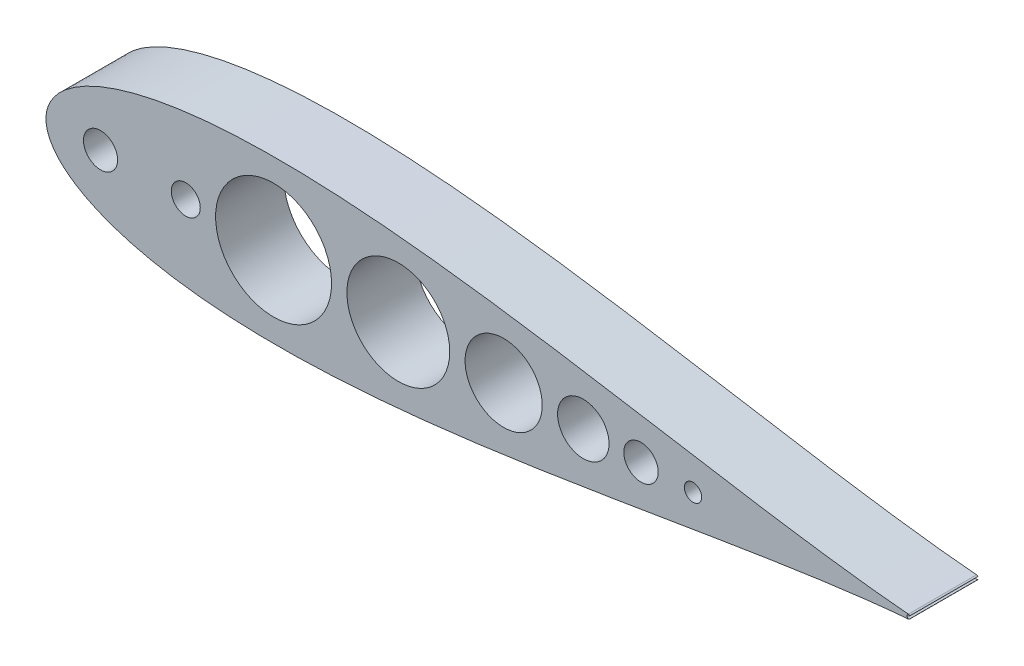
SolidWorks part; units mm, degrees
material "Polyurethane Foam Rigid"
ref_plane "Front Plane" through (0, 0, 0) normal (0, 0, 1) x (1, 0, 0)
ref_plane "Top Plane" through (0, 0, 0) normal (0, 1, 0) x (1, 0, 0)
ref_plane "Right Plane" through (0, 0, 0) normal (1, 0, 0) x (0, 0, -1)
curve "Curve4"
  spline degree 3 poles (100, 0, 0) (99.8498, 0.0023, 0) (99.4759, 0.008, 0) (99.1023, 0.0238, 0) (98.8789, 0.0332, 0) knots 0 0 0 0 0.401829 1 1 1 1
curve "Curve5"
  spline degree 3 poles (99.3714, -0.0082, 0) (100.2526, 0, 0) (99.3714, 0.0082, 0) (98.8504, 0.035, 0) (97.904, 0.0811, 0) (96.8285, 0.1543, 0) (95.5159, 0.2583, 0) (94.013, 0.3972, 0) (92.313, 0.574, 0) (90.4281, 0.791, 0) (88.3655, 1.0495, 0) (86.1348, 1.3497, 0) (83.7456, 1.691, 0) (81.2082, 2.0715, 0) (78.5335, 2.4886, 0) (75.7326, 2.9386, 0) (72.8172, 3.4168, 0) (69.799, 3.9177, 0) (66.6904, 4.435, 0) (63.5039, 4.9616, 0) (60.2521, 5.4899, 0) (56.948, 6.0119, 0) (53.6049, 6.519, 0) (50.2363, 7.0024, 0) (46.8558, 7.4534, 0) (43.4774, 7.8632, 0) (40.1152, 8.2232, 0) (36.7837, 8.5249, 0) (33.4975, 8.7606, 0) (30.2716, 8.923, 0) (27.1211, 9.0055, 0) (24.0614, 9.0025, 0) (21.108, 8.909, 0) (18.277, 8.7213, 0) (15.5843, 8.4369, 0) (13.0466, 8.0543, 0) (10.6806, 7.5735, 0) (8.5039, 6.996, 0) (6.5349, 6.3253, 0) (4.7933, 5.5673, 0) (3.3001, 4.7321, 0) (2.0777, 3.8366, 0) (1.1467, 2.91, 0) (0.5165, 2.0014, 0) (0.165, 1.1816, 0) (0.0231, 0.524, 0) (-0.0093, 0, 0) (0.0231, -0.524, 0) (0.165, -1.1816, 0) (0.5165, -2.0014, 0) (1.1467, -2.91, 0) (2.0777, -3.8366, 0) (3.3001, -4.7321, 0) (4.7933, -5.5673, 0) (6.5349, -6.3253, 0) (8.5039, -6.996, 0) (10.6806, -7.5735, 0) (13.0466, -8.0543, 0) (15.5843, -8.4369, 0) (18.277, -8.7213, 0) (21.108, -8.909, 0) (24.0614, -9.0025, 0) (27.1211, -9.0055, 0) (30.2716, -8.923, 0) (33.4975, -8.7606, 0) (36.7837, -8.5249, 0) (40.1152, -8.2232, 0) (43.4774, -7.8632, 0) (46.8558, -7.4534, 0) (50.2363, -7.0024, 0) (53.6049, -6.519, 0) (56.948, -6.0119, 0) (60.2521, -5.4899, 0) (63.5039, -4.9616, 0) (66.6904, -4.435, 0) (69.799, -3.9177, 0) (72.8172, -3.4168, 0) (75.7326, -2.9386, 0) (78.5335, -2.4886, 0) (81.2082, -2.0715, 0) (83.7456, -1.691, 0) (86.1348, -1.3497, 0) (88.3655, -1.0495, 0) (90.4281, -0.791, 0) (92.313, -0.574, 0) (94.013, -0.3972, 0) (95.5159, -0.2583, 0) (96.8285, -0.1543, 0) (97.904, -0.0811, 0) (98.8504, -0.035, 0) (99.3714, -0.0082, 0) (100.2526, 0, 0) (99.3714, 0.0082, 0) knots -0.009667 -0.005395 -0.002168 0 0.002168 0.005395 0.009667 0.014967 0.021271 0.028553 0.036781 0.04592 0.055932 0.066773 0.078397 0.090755 0.103793 0.117456 0.131686 0.146422 0.1616 0.177156 0.193024 0.209135 0.225421 0.241812 0.258238 0.274629 0.290914 0.307025 0.322893 0.338448 0.353626 0.368361 0.38259 0.396253 0.40929 0.421647 0.43327 0.444109 0.454119 0.463255 0.471479 0.478755 0.485052 0.490344 0.49461 0.497833 0.5 0.502167 0.50539 0.509656 0.514948 0.521245 0.528521 0.536745 0.545881 0.555891 0.56673 0.578353 0.59071 0.603747 0.61741 0.631639 0.646374 0.661552 0.677107 0.692975 0.709086 0.725371 0.741762 0.758188 0.774579 0.790865 0.806976 0.822844 0.8384 0.853578 0.868314 0.882544 0.896207 0.909245 0.921603 0.933227 0.944068 0.95408 0.963219 0.971447 0.978729 0.985033 0.990333 0.994605 0.997832 1 1.002168 1.005395 1.009667 periodic
sketch "Sketch2" plane through (0, 0, 0) normal (0, 0, 1) x (1, 0, 0)
  line L0 (100, 0) -> (0, 0) construction
  line L1 (1.2169, -991.9959) -> (1.2169, 49008.0041) construction
  line L2 (93.345, 0) -> (114.935, 0) construction
  line L3 (125.634, 0) -> (131.6629, 0) construction
  line L4 (643.5991, 0) -> (643.5991, -1.016)
  line L9 (0, 0) -> (643.9668, 0)
  line L13 (460.661, 0) -> (473.361, 0)
  circle A0 centre (104.14, 0) radius 10.795 construction
  arc A1 (1.2169, -4.6585) -> (1.2169, 4.6585) centre (9.525, 0) cw
  arc A2 (641.5671, 0) -> (644.1071, 0) centre (642.8371, 0) ccw
  circle A4 centre (104.14, 0) radius 10.795
  circle A9 centre (40.64, 0) radius 12.7
  circle A14 centre (642.3793, 0) radius 1.5875 construction
  arc A15 (642.5108, -1.582) -> (642.5108, 1.582) centre (642.3793, 0) ccw
  spline S2 degree 3 poles (666.3448, -0.0547) (672.2538, 0) (666.3448, 0.0547) (662.8509, 0.2344) (656.505, 0.5436) (649.293, 1.0348) (640.4916, 1.7319) (630.4138, 2.6634) (619.0141, 3.8493) (606.375, 5.3044) (592.5439, 7.0376) (577.5855, 9.0506) (561.5643, 11.3389) (544.5497, 13.8907) (526.6141, 16.6877) (507.8326, 19.7051) (488.2827, 22.9117) (468.0444, 26.2704) (447.1994, 29.739) (425.8316, 33.2703) (404.0263, 36.8132) (381.8707, 40.3133) (359.4533, 43.7135) (336.8645, 46.9554) (314.1962, 49.9798) (291.5418, 52.7277) (268.9963, 55.1412) (246.6566, 57.1646) (224.6209, 58.7452) (202.9892, 59.8341) (181.8631, 60.3875) (161.3458, 60.367) (141.542, 59.7399) (122.5581, 58.4818) (104.5023, 56.5743) (87.485, 54.0089) (71.6197, 50.7848) (57.0237, 46.9125) (43.8205, 42.415) (32.1416, 37.3322) (22.1291, 31.7315) (13.9324, 25.7264) (7.6896, 19.5132) (3.4631, 13.4204) (1.1063, 7.9234) (0.1546, 3.5138) (-0.0622, 0) (0.1546, -3.5138) (1.1063, -7.9234) (3.4631, -13.4204) (7.6896, -19.5132) (13.9324, -25.7264) (22.1291, -31.7315) (32.1416, -37.3322) (43.8205, -42.415) (57.0237, -46.9125) (71.6197, -50.7848) (87.485, -54.0089) (104.5023, -56.5743) (122.5581, -58.4818) (141.542, -59.7399) (161.3458, -60.367) (181.8631, -60.3875) (202.9892, -59.8341) (224.6209, -58.7452) (246.6566, -57.1646) (268.9963, -55.1412) (291.5418, -52.7277) (314.1962, -49.9798) (336.8645, -46.9554) (359.4533, -43.7135) (381.8707, -40.3133) (404.0263, -36.8132) (425.8316, -33.2703) (447.1994, -29.739) (468.0444, -26.2704) (488.2827, -22.9117) (507.8326, -19.7051) (526.6141, -16.6877) (544.5497, -13.8907) (561.5643, -11.3389) (577.5855, -9.0506) (592.5439, -7.0376) (606.375, -5.3044) (619.0141, -3.8493) (630.4138, -2.6634) (640.4916, -1.7319) (649.293, -1.0348) (656.505, -0.5436) (662.8509, -0.2344) (666.3448, -0.0547) (672.2538, 0) (666.3448, 0.0547) knots -0.009667 -0.005395 -0.002168 0 0.002168 0.005395 0.009667 0.014967 0.021271 0.028553 0.036781 0.04592 0.055932 0.066773 0.078397 0.090755 0.103793 0.117456 0.131686 0.146422 0.1616 0.177156 0.193024 0.209135 0.225421 0.241812 0.258238 0.274629 0.290914 0.307025 0.322893 0.338448 0.353626 0.368361 0.38259 0.396253 0.40929 0.421647 0.43327 0.444109 0.454119 0.463255 0.471479 0.478755 0.485052 0.490344 0.49461 0.497833 0.5 0.502167 0.50539 0.509656 0.514948 0.521245 0.528521 0.536745 0.545881 0.555891 0.56673 0.578353 0.59071 0.603747 0.61741 0.631639 0.646374 0.661552 0.677107 0.692975 0.709086 0.725371 0.741762 0.758188 0.774579 0.790865 0.806976 0.822844 0.8384 0.853578 0.868314 0.882544 0.896207 0.909245 0.921603 0.933227 0.944068 0.95408 0.963219 0.971447 0.978729 0.985033 0.990333 0.994605 0.997832 1 1.002168 1.005395 1.009667 only from (670.56, 0) to (670.56, 0)
  point P2 (167.64, 0)
  point P8 (1.2169, -4.6585)
  point P10 (1.2169, 4.6585)
  point P28 (133.9182, 0)
  point P49 (130.0977, 0)
  point P59 (95.1064, 0)
  dimension "D2" = 21.59
  dimension "D3" = 1.016
  dimension "D4" = 1.27
  dimension "D8" = 25.4
  dimension "D9" = 63.5
  dimension "D10" = 3.175
  dimension "D1" = 167.64
  dimension "D6" = 63.5
extrude "Boss-Extrude1" add sketch "Sketch2" along normal blind 50.8
sketch "Sketch3" plane through (0, 0, 50.8) normal (0, 0, 1) x (1, 0, 0)
  line L0 (84.14, -12.7) -> (62.637, -12.7) construction
  line L1 (430.4749, -1041.2705) -> (430.4749, 48958.7295) construction
  line L2 (114.935, 0) -> (641.5671, 0) construction
  line L3 (27.94, 0) -> (0, 0)
  line L4 (641.5671, 0) -> (114.935, 0)
  line L5 (93.345, 0) -> (53.34, 0)
  line L6 (27.94, 0) -> (0, 0)
  line L7 (212.768, -1000) -> (212.768, 49000) construction
  line L8 (93.345, 0) -> (53.34, 0)
  line L9 (224.198, -1000) -> (224.198, 49000) construction
  line L10 (300.8092, -1000) -> (300.8092, 49000) construction
  line L11 (312.2392, -1000) -> (312.2392, 49000) construction
  line L12 (369.7207, -1000) -> (369.7207, 49000) construction
  line L13 (93.345, -17.145) -> (65.0689, -17.145) construction
  line L14 (419.5047, -1000) -> (419.5047, 49000) construction
  line L15 (126.365, -1000) -> (126.365, 49000) construction
  line L16 (381.1507, -1000) -> (381.1507, 49000) construction
  line L17 (52.7726, -27.2676) -> (52.7726, -27.2676) construction
  arc A0 (36.4352, -25.0495) -> (62.637, -12.7) centre (40.64, 0) ccw construction
  circle A2 centre (169.5665, 0) radius 43.2015
  arc A3 (642.5108, -1.582) -> (643.5991, -1.016) centre (642.3793, 0) ccw
  arc A4 (93.345, 0) -> (114.935, 0) centre (104.14, 0) ccw
  arc A5 (27.94, 0) -> (53.34, 0) centre (40.64, 0) ccw
  arc A6 (642.5108, -1.582) -> (643.5991, -1.016) centre (642.3793, 0) ccw
  circle A7 centre (262.5036, 0) radius 38.3056
  arc A8 (27.94, 0) -> (53.34, 0) centre (40.64, 0) ccw
  circle A9 centre (340.9799, 0) radius 28.7408
  circle A10 centre (400.3277, 0) radius 19.177
  circle A11 centre (443.3019, 0) radius 12.827
  circle A12 centre (482.0825, 0) radius 6.477
  arc A13 (52.7726, -27.2676) -> (65.0689, -17.145) centre (40.64, 0) ccw construction
  arc A14 (638.2053, 15.2585) -> (638.2053, 15.2585) centre (638.2053, 15.2585) ccw construction
  arc A18 (641.5671, 0) -> (643.5991, -1.016) centre (642.8371, 0) ccw
  arc A19 (641.5671, 0) -> (643.5991, -1.016) centre (642.8371, 0) ccw
  spline S1 degree 3 poles (1488.1541, -2580.0534) (314.1987, 184.2642) (-15.4092, 68.5977) (1.1063, -7.9234) (3.4631, -13.4204) (7.6896, -19.5132) (13.9324, -25.7264) (22.1291, -31.7315) (32.1416, -37.3322) (43.8205, -42.415) (57.0237, -46.9125) (71.6197, -50.7848) (87.485, -54.0089) (104.5023, -56.5743) (122.5581, -58.4818) (141.542, -59.7399) (161.3458, -60.367) (181.8631, -60.3875) (202.9892, -59.8341) (224.6209, -58.7452) (246.6566, -57.1646) (268.9963, -55.1412) (291.5418, -52.7277) (314.1962, -49.9798) (336.8645, -46.9554) (359.4533, -43.7135) (381.8707, -40.3133) (404.0263, -36.8132) (425.8316, -33.2703) (447.1994, -29.739) (468.0444, -26.2704) (488.2827, -22.9117) (507.8326, -19.7051) (526.6141, -16.6877) (544.5497, -13.8907) (561.5643, -11.3389) (577.5855, -9.0506) (592.5439, -7.0376) (606.375, -5.3044) (619.0141, -3.8493) (630.4138, -2.6634) (754.7119, 8.8252) (895.5191, -9.0089) (-2343.84, -283.812) knots 0.342093 0.342093 0.342093 0.342093 0.502167 0.50539 0.509656 0.514948 0.521245 0.528521 0.536745 0.545881 0.555891 0.56673 0.578353 0.59071 0.603747 0.61741 0.631639 0.646374 0.661552 0.677107 0.692975 0.709086 0.725371 0.741762 0.758188 0.774579 0.790865 0.806976 0.822844 0.8384 0.853578 0.868314 0.882544 0.896207 0.909245 0.921603 0.933227 0.944068 0.95408 0.963219 0.971447 0.978729 1.23227 1.23227 1.23227 1.23227 only from (0, 0) to (642.5108, -1.582)
  spline S2 degree 3 poles (0, 0) (0, -1.0075) (0.1546, -3.5138) (1.1063, -7.9234) (3.4631, -13.4204) (7.6896, -19.5132) (13.9324, -25.7264) (22.1291, -31.7315) (32.1416, -37.3322) (43.8205, -42.415) (57.0237, -46.9125) (71.6197, -50.7848) (87.485, -54.0089) (104.5023, -56.5743) (122.5581, -58.4818) (141.542, -59.7399) (161.3458, -60.367) (181.8631, -60.3875) (202.9892, -59.8341) (224.6209, -58.7452) (246.6566, -57.1646) (268.9963, -55.1412) (291.5418, -52.7277) (314.1962, -49.9798) (336.8645, -46.9554) (359.4533, -43.7135) (381.8707, -40.3133) (404.0263, -36.8132) (425.8316, -33.2703) (447.1994, -29.739) (468.0444, -26.2704) (488.2827, -22.9117) (507.8326, -19.7051) (526.6141, -16.6877) (544.5497, -13.8907) (561.5643, -11.3389) (577.5855, -9.0506) (592.5439, -7.0376) (606.375, -5.3044) (619.0141, -3.8493) (630.4138, -2.6634) (638.0937, -1.9535) (641.9934, -1.6251) (642.5108, -1.582) knots 0.5 0.5 0.5 0.5 0.502167 0.50539 0.509656 0.514948 0.521245 0.528521 0.536745 0.545881 0.555891 0.56673 0.578353 0.59071 0.603747 0.61741 0.631639 0.646374 0.661552 0.677107 0.692975 0.709086 0.725371 0.741762 0.758188 0.774579 0.790865 0.806976 0.822844 0.8384 0.853578 0.868314 0.882544 0.896207 0.909245 0.921603 0.933227 0.944068 0.95408 0.963219 0.971447 0.978729 0.979843 0.979843 0.979843 0.979843
  spline S4 degree 1 poles (52.7726, -27.2676) (638.2053, 15.2585) knots 0 0 1 1 construction
  spline S5 degree 3 poles (52.7726, -27.2676) (54.098, -27.7509) (56.7529, -28.6784) (62.1794, -30.4243) (69.1006, -32.3953) (77.5892, -34.4571) (89.0862, -36.8389) (103.7331, -39.1926) (125.3657, -41.6037) (144.2709, -42.7116) (163.2853, -43.1964) (177.6693, -43.2555) (201.2447, -42.8023) (227.4371, -41.4675) (254.4928, -39.2877) (277.8401, -36.9937) (301.0423, -34.3583) (330.3789, -30.5811) (368.329, -25.1309) (404.83, -19.3409) (435.2358, -14.3425) (451.6826, -11.6119) (464.2574, -9.5208) (476.8398, -7.4307) (497.3171, -4.0443) (526.9629, 0.7645) (562.929, 6.2684) (594.1055, 10.5252) (616.0859, 13.0867) (628.694, 14.3901) (635.0364, 14.9826) (638.2053, 15.2585) knots 0.548481 0.548481 0.548481 0.548481 0.551835 0.555189 0.561898 0.568606 0.575315 0.588731 0.602148 0.62409 0.630798 0.644215 0.655815 0.682649 0.701659 0.715076 0.733763 0.752449 0.779283 0.816817 0.832298 0.845715 0.852722 0.859728 0.873145 0.897318 0.924152 0.950985 0.964402 0.971111 0.977819 0.977819 0.977819 0.977819 construction
  line M19 (641.5671, 0) -> (114.935, 0)
  dimension "D3" = 11.43
  dimension "D7" = 38.354
  dimension "D8" = 25.654
  dimension "D9" = 12.954
  dimension "D4" = 11.43
  dimension "D5" = 11.43
  dimension "D6" = 11.43
  dimension "D1" = 0
  dimension "D10" = 17.145
extrude "Cut-Extrude2" cut sketch "Sketch3" against normal through all both and the other way through all contours A2 M19 | A7 M19 | A9 M19 | A10 M19 | A11 M19 | A12 M19
mirror "Mirror1" about plane through (0, 0, 0) normal (0, 1, 0) of "Cut-Extrude2", "Boss-Extrude1"
equation "\"0.5n\"=0"
